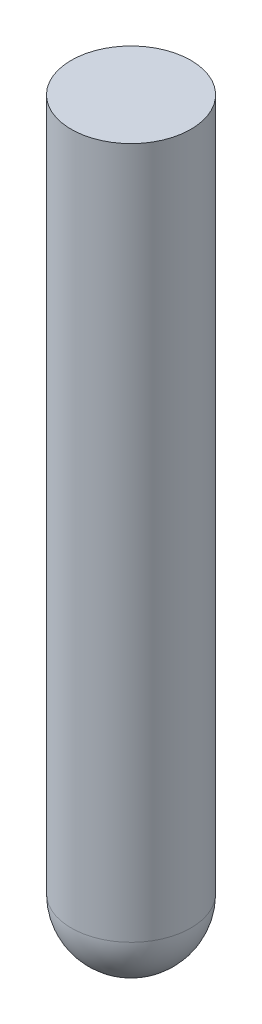
SolidWorks part; units mm, degrees
ref_plane "Front Plane" through (0, 0, 0) normal (0, 0, 1) x (1, 0, 0)
ref_plane "Top Plane" through (0, 0, 0) normal (0, 1, 0) x (1, 0, 0)
ref_plane "Right Plane" through (0, 0, 0) normal (1, 0, 0) x (0, 0, -1)
sketch "Sketch1" plane through (0, 0, 0) normal (1, 0, 0) x (0, 0, -1)
  line L0 (75.6999, 32.1246) -> (75.6999, 26.3431)
sweep "Sweep1" add path "Sketch1" circular profile diameter 1 parameters "D3"=1
sketch "Sketch14" plane through (0, 0, 0) normal (1, 0, 0) x (0, 0, -1)
  line L0 (75.1999, 26.3431) -> (76.1999, 26.3431) construction
  line L1 (75.6999, 26.8431) -> (75.6999, 25.8431) construction
  line L2 (75.6999, 26.8431) -> (75.6999, 25.8431)
  arc A0 (75.6999, 26.8431) -> (75.6999, 25.8431) centre (75.6999, 26.3431) ccw
revolve "Revolve4" add sketch "Sketch14" angle 360 about L1
